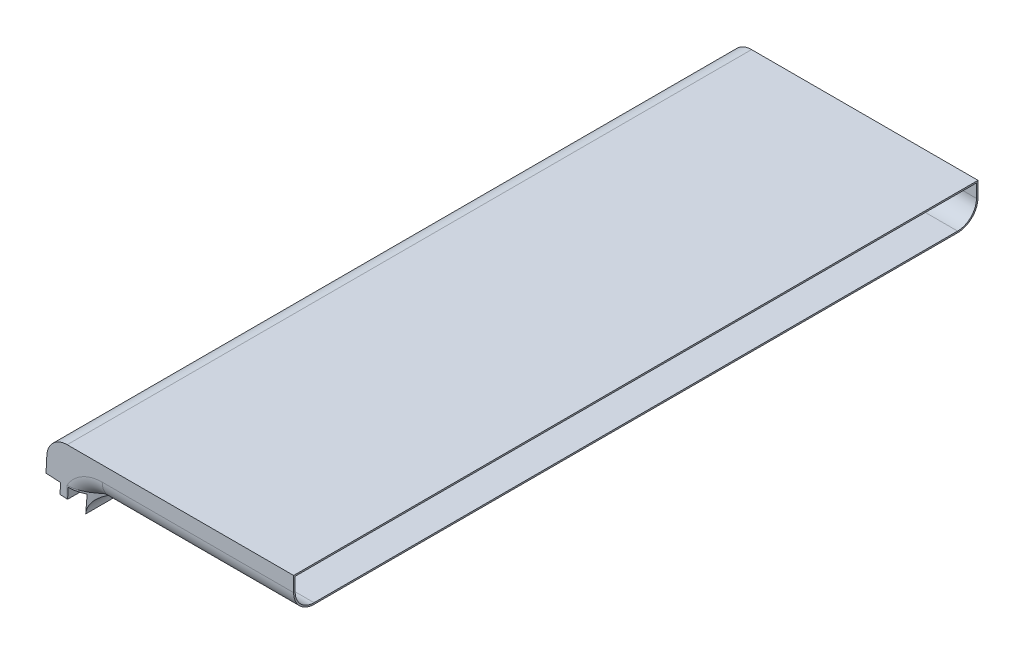
SolidWorks part; units mm, degrees
ref_plane "Front Plane" through (0, 0, 0) normal (0, 0, 1) x (1, 0, 0)
ref_plane "Top Plane" through (0, 0, 0) normal (0, 1, 0) x (1, 0, 0)
ref_plane "Right Plane" through (0, 0, 0) normal (1, 0, 0) x (0, 0, -1)
sketch "Sketch2" plane through (0, 0, 0) normal (0, 0, 1) x (1, 0, 0)
  line L0 (0, 0) -> (162.8209, 0)
  line L1 (162.8209, 0) -> (162.8209, 23.2)
  line L2 (162.8209, 23.2) -> (1.2159, 23.2)
  line L3 (1.2159, 23.2) -> (0, 0)
  dimension "D1" = 161.605
  dimension "D2" = 87
  dimension "D3" = 23.2
extrude "Boss-Extrude1" add sketch "Sketch2" along normal blind 450
fillet "Fillet1" radius 13.4 1 edges at (1.2159, 23.2, 225)
sketch "Sketch4" plane through (0, 0, 450) normal (0, 0, 1) x (1, 0, 0)
  line L0 (0, 0) -> (-1.4713, -28.0745) construction
  line L1 (0.5503, 10.5013) -> (0, 0) construction
  line L3 (24.1668, -1.2665) -> (23.5677, -12.6987)
  line L4 (0, 0) -> (36.9493, 0)
  line L5 (0, 0) -> (162.8209, 0) construction
  line L6 (0, 0) -> (24.1668, -1.2665) construction
  line L7 (0, 0) -> (9.5868, -0.5024)
  line L8 (9.5868, -0.5024) -> (9.2205, -7.4928)
  line L9 (9.2205, -7.4928) -> (14.2136, -7.7545)
  line L10 (14.2136, -7.7545) -> (14.58, -0.7641)
  line L11 (14.58, -0.7641) -> (24.1668, -1.2665)
  arc A0 (36.9493, 0) -> (23.5677, -12.6987) centre (36.9493, -13.4) ccw
  dimension "D1" = 13.4
  dimension "D2" = 5
  dimension "D3" = 7
  dimension "D4" = 3
  dimension "D5" = 24.2
extrude "Boss-Extrude2" add sketch "Sketch4" against normal through all
fillet "Fillet2" radius 13.4 4 edges at (27.7254, -3.68, 0) (27.7254, -3.68, 450) (99.8851, 0, 450) (99.8851, 0, 0)
sketch "Sketch5" plane through (0, 0, 0) normal (0, 0, 1) x (1, 0, 0)
  line L0 (0, 0) -> (-1.4713, -28.0745) construction
  line L3 (24.1668, -1.2665) -> (23.5677, -12.6987)
  line L4 (0, 0) -> (36.9493, 0)
  line L6 (0, 0) -> (24.1668, -1.2665) construction
  line L7 (0, 0) -> (9.5868, -0.5024)
  line L8 (9.5868, -0.5024) -> (9.2205, -7.4928)
  line L9 (9.2205, -7.4928) -> (14.2136, -7.7545)
  line L10 (14.2136, -7.7545) -> (14.58, -0.7641)
  line L11 (14.58, -0.7641) -> (24.1668, -1.2665)
  arc A0 (36.9493, 0) -> (23.5677, -12.6987) centre (36.9493, -13.4) ccw
  dimension "D1" = 13.4
  dimension "D2" = 5
  dimension "D3" = 7
  dimension "D4" = 3
  dimension "D5" = 24.2
extrude "Cut-Extrude1" cut sketch "Sketch5" along normal through all
shell "Shell1" thickness 1
sketch "Sketch6" plane through (0, 0, 0) normal (0, 0, 1) x (1, 0, 0)
  line L0 (0, 0) -> (-1.4713, -28.0745) construction
  line L3 (24.1668, -1.2665) -> (23.5677, -12.6987)
  line L4 (0, 0) -> (36.9493, 0)
  line L6 (0, 0) -> (24.1668, -1.2665) construction
  line L7 (0, 0) -> (9.5868, -0.5024)
  line L8 (9.5868, -0.5024) -> (9.2205, -7.4928)
  line L9 (9.2205, -7.4928) -> (14.2136, -7.7545)
  line L10 (14.2136, -7.7545) -> (14.58, -0.7641)
  line L11 (14.58, -0.7641) -> (24.1668, -1.2665)
  arc A0 (36.9493, 0) -> (23.5677, -12.6987) centre (36.9493, -13.4) ccw
  dimension "D1" = 13.4
  dimension "D2" = 5
  dimension "D3" = 7
  dimension "D4" = 3
  dimension "D5" = 24.2
extrude "Boss-Extrude3" add sketch "Sketch6" along normal up to surface (450 mm away) up to face at (55.2121, 12.7829, 450)
sketch "Sketch7" plane through (0, 0, 0) normal (0, -1, 0) x (1, 0, 0)
  line L0 (13.7399, 450) -> (36.9493, 450)
  line L1 (36.9493, 450) -> (36.9493, 436.6)
  line L2 (36.9493, 13.4) -> (36.9493, 0)
  line L3 (162.8209, 0) -> (36.9493, 0) construction
  line L4 (36.9493, 13.4) -> (36.9493, 0) construction
  line L5 (36.9493, 0) -> (13.7399, 0)
  spline S0 degree 3 poles (-248.1857, -515.0858) (-77.3187, 351.0795) (-21.5401, 456.7939) (17.7261, 449.5782) (18.2854, 449.4508) (19.3971, 449.1501) (19.9513, 448.9762) (22.6674, 448.0117) (24.6889, 446.9373) (27.0884, 445.3395) (27.5609, 445.0076) (28.4876, 444.3262) (28.9427, 443.9762) (30.2867, 442.9021) (31.1547, 442.1541) (32.8532, 440.6158) (33.6837, 439.8255) (68.3922, 405.9657) (88.9167, 352.0856) (425.6991, 1357.9369) knots -4.172059 -4.172059 -4.172059 -4.172059 0.125 0.125 0.1875 0.1875 0.25 0.25 0.5 0.5 0.5625 0.5625 0.625 0.625 0.75 0.75 0.875 0.875 6.033722 6.033722 6.033722 6.033722 only from (13.7399, 450) to (36.9493, 436.6) construction
  spline S1 degree 3 poles (425.6997, -907.9387) (88.9167, 97.9145) (68.3922, 44.0343) (33.6837, 10.1745) (32.8532, 9.3842) (31.1547, 7.8459) (30.2867, 7.0979) (28.9427, 6.0238) (28.4876, 5.6738) (27.5609, 4.9924) (27.0884, 4.6605) (24.6889, 3.0627) (22.6674, 1.9883) (19.9513, 1.0238) (19.3971, 0.8499) (18.2854, 0.5492) (17.7261, 0.4218) (-21.5398, -6.7938) (-77.318, 98.9191) (-248.1824, 965.0692) knots -5.033725 -5.033725 -5.033725 -5.033725 0.125 0.125 0.25 0.25 0.375 0.375 0.4375 0.4375 0.5 0.5 0.75 0.75 0.8125 0.8125 0.875 0.875 5.172032 5.172032 5.172032 5.172032 only from (36.9493, 13.4) to (13.7399, 0) construction
  spline S2 degree 3 poles (13.7399, 450) (14.897, 450) (16.0373, 449.8886) (17.7261, 449.5782) (18.2854, 449.4508) (19.3971, 449.1501) (19.9513, 448.9762) (22.6674, 448.0117) (24.6889, 446.9373) (27.0884, 445.3395) (27.5609, 445.0076) (28.4876, 444.3262) (28.9427, 443.9762) (30.2867, 442.9021) (31.1547, 442.1541) (32.8532, 440.6158) (33.6837, 439.8255) (35.3259, 438.2234) (36.1392, 437.4101) (36.9493, 436.6) knots 0 0 0 0 0.125 0.125 0.1875 0.1875 0.25 0.25 0.5 0.5 0.5625 0.5625 0.625 0.625 0.75 0.75 0.875 0.875 1 1 1 1
  spline S3 degree 3 poles (36.9493, 13.4) (36.1392, 12.5899) (35.3259, 11.7766) (33.6837, 10.1745) (32.8532, 9.3842) (31.1547, 7.8459) (30.2867, 7.0979) (28.9427, 6.0238) (28.4876, 5.6738) (27.5609, 4.9924) (27.0884, 4.6605) (24.6889, 3.0627) (22.6674, 1.9883) (19.9513, 1.0238) (19.3971, 0.8499) (18.2854, 0.5492) (17.7261, 0.4218) (16.0373, 0.1114) (14.897, 0) (13.7399, 0) knots 0 0 0 0 0.125 0.125 0.25 0.25 0.375 0.375 0.4375 0.4375 0.5 0.5 0.75 0.75 0.8125 0.8125 0.875 0.875 1 1 1 1
extrude "Cut-Extrude2" cut sketch "Sketch7" along normal through all
